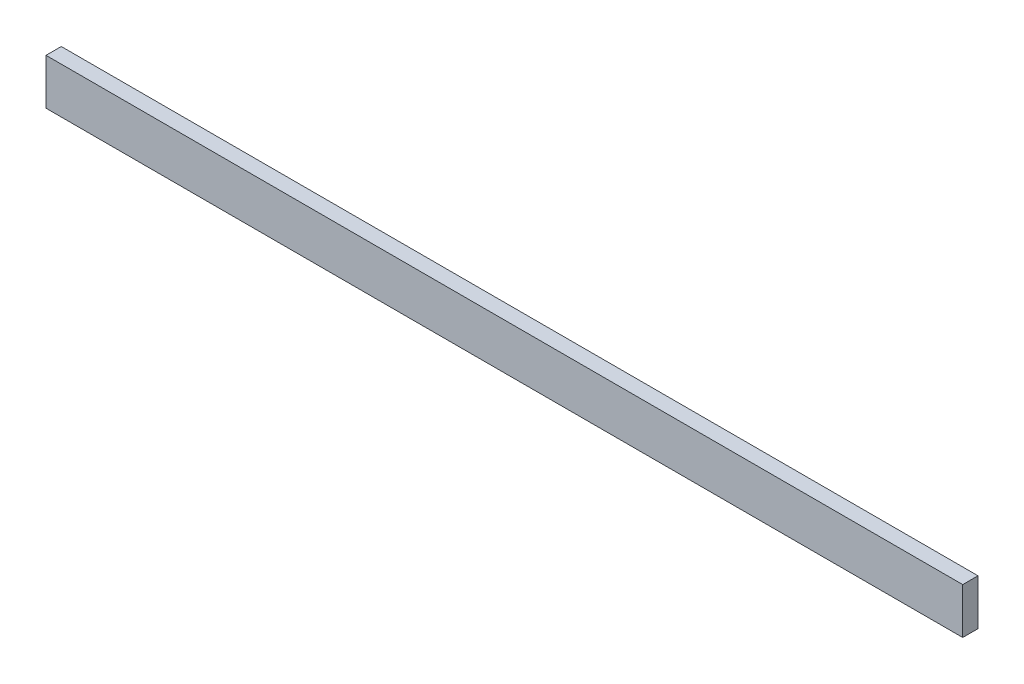
SolidWorks part; units mm, degrees
ref_plane "Front Plane" through (0, 0, 0) normal (0, 0, 1) x (1, 0, 0)
ref_plane "Top Plane" through (0, 0, 0) normal (0, 1, 0) x (1, 0, 0)
ref_plane "Right Plane" through (0, 0, 0) normal (1, 0, 0) x (0, 0, -1)
sketch "Sketch1" plane through (0, 0, 0) normal (0, 0, 1) x (1, 0, 0)
  line L1 (-66.6093, 63) -> (695.3907, 63)
  line L2 (-66.6093, 63) -> (-66.6093, 24.9)
  line L3 (-66.6093, 24.9) -> (695.3907, 24.9)
  line L4 (695.3907, 63) -> (695.3907, 24.9)
  dimension "D1" = 762
  dimension "D2" = 38.1
extrude "Boss-Extrude1" add sketch "Sketch1" along normal blind 12.7
